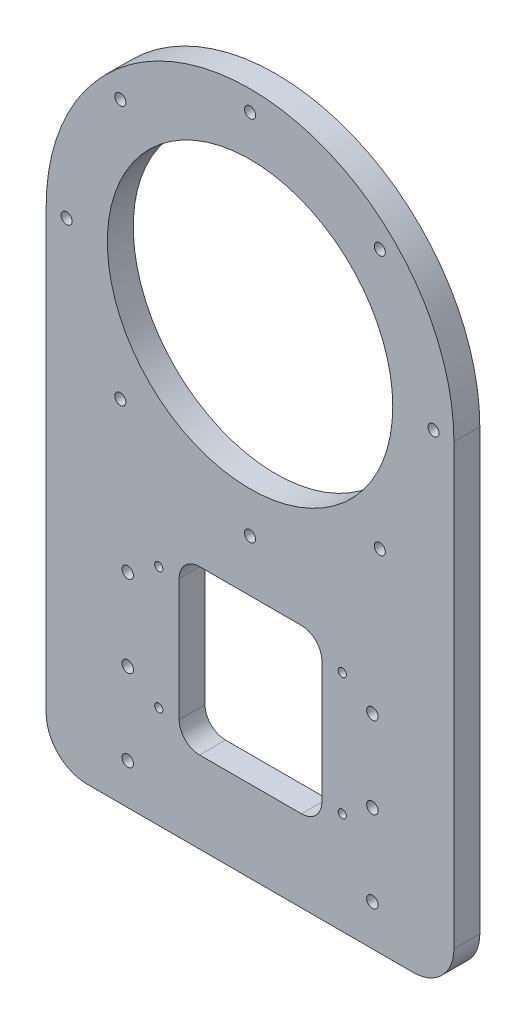
SolidWorks part; units mm, degrees
ref_plane "Front Plane" through (0, 0, 0) normal (0, 0, 1) x (1, 0, 0)
ref_plane "Top Plane" through (0, 0, 0) normal (0, 1, 0) x (1, 0, 0)
ref_plane "Right Plane" through (0, 0, 0) normal (1, 0, 0) x (0, 0, -1)
sketch "Sketch1" plane through (0, 0, 0) normal (0, 0, 1) x (1, 0, 0)
  circle A0 centre (0, 0) radius 35
  circle A1 centre (0, 0) radius 50
  dimension "D1" = 70
  dimension "D2" = 100
extrude "Boss-Extrude1" add sketch "Sketch1" along normal blind 6.35
sketch "Sketch2" plane through (0, 0, 6.35) normal (0, 0, 1) x (1, 0, 0)
  circle A0 centre (0, 0) radius 105
  dimension "D1" = 210
sketch "Sketch3" plane through (0, 0, 6.35) normal (0, 0, 1) x (1, 0, 0)
  line L0 (-50, 0) -> (-50, -117.7)
  line L1 (-50, -117.7) -> (50, -117.7)
  line L4 (0, -105) -> (0, -117.7) construction
  line L6 (137.4941, -68.35) -> (137.4941, -66.7834)
  line L14 (50, 0) -> (50, -117.7)
  circle A0 centre (0, 0) radius 50 construction
  circle A2 centre (0, 0) radius 105 construction
  arc A3 (-50, 0) -> (50, 0) centre (0, 0) ccw
  dimension "D3" = 12.7
extrude "Boss-Extrude2" add sketch "Sketch3" against normal up to surface (6.35 mm away) up to face at (50, 0, 0)
sketch "Sketch4" plane through (0, 0, 6.35) normal (0, 0, 1) x (1, 0, 0)
  circle A0 centre (0, 0) radius 35 construction
  point P0 (45, 0)
  point P3 (31.8198, -31.8198)
  point P6 (0, -45)
  point P7 (-31.8198, -31.8198)
  point P8 (-45, 0)
  point P9 (-31.8198, 31.8198)
  point P10 (0, 45)
  point P11 (31.8198, 31.8198)
  point P12 (0, 0)
  dimension "D1" = 45
  dimension "D2" = 8
hole_wizard "#6-32 Tapped Hole1" positions "Sketch5" profile "Sketch6" tap size "#6-32" standard "ANSI Inch" end condition through all
sketch "Sketch5" plane through (0, 0, 6.35) normal (0, 0, 1) x (1, 0, 0)
  point P0 (-45, 0)
  point P3 (-31.8198, -31.8198)
  point P6 (0, -45)
  point P9 (31.8198, -31.8198)
  point P12 (45, 0)
  point P15 (31.8198, 31.8198)
  point P18 (0, 45)
  point P21 (-31.8198, 31.8198)
sketch "Sketch6" plane through (-45, 0, 6.35) normal (1, 0, 0) x (0, -1, 0)
  line L0 (0, 0) -> (0, 6.35)
  line L1 (0, 6.35) -> (1.3525, 6.35)
  line L2 (1.3525, 6.35) -> (1.3525, 0)
  line L5 (1.3525, 0) -> (0, 0)
  line L11 (0, -6.35) -> (0, 107.95) construction
  dimension "Thru Tap Drill Dia." = 2.7051
  dimension "Thru Tap Drill Depth" = 6.35
cosmetic thread "Hole Thread1" parameters "D2"=3.5052
cosmetic thread "Hole Thread2" parameters "D2"=3.5052
cosmetic thread "Hole Thread3" parameters "D2"=3.5052
cosmetic thread "Hole Thread4" parameters "D2"=3.5052
cosmetic thread "Hole Thread5" parameters "D2"=3.5052
cosmetic thread "Hole Thread6" parameters "D2"=3.5052
cosmetic thread "Hole Thread7" parameters "D2"=3.5052
cosmetic thread "Hole Thread8" parameters "D2"=3.5052
fillet "Fillet1" radius 10 2 edges at (50, -117.7, 3.175) (-50, -117.7, 3.175)
sketch "Sketch7" plane through (0, 0, 6.35) normal (0, 0, 1) x (1, 0, 0)
  line L0 (0, -105) -> (0, -117.7) construction
  line L1 (-50, -117.7) -> (50, -117.7) construction
  point P0 (-30, -107.7)
  point P1 (30, -107.7)
  point P6 (-30, -67.7)
  point P7 (-30, -87.7)
  point P8 (30, -87.7)
  point P9 (30, -67.7)
  dimension "D1" = 60
  dimension "D2" = 30
  dimension "D3" = 10
  dimension "D4" = 10
  dimension "D5" = 2
  dimension "D6" = 2
hole_wizard "M4x0.7 Tapped Hole1" positions "Sketch8" profile "Sketch10" tap size "M4x0.7" standard "ANSI Metric" end condition through all
sketch "Sketch8" plane through (0, 0, 6.35) normal (0, 0, 1) x (1, 0, 0)
  point P0 (-30, -107.7)
  point P3 (30, -107.7)
  point P6 (30, -87.7)
  point P9 (-30, -87.7)
  point P13 (30, -67.7)
  point P16 (-30, -67.7)
sketch "Sketch10" plane through (-30, -107.7, 6.35) normal (1, 0, 0) x (0, -1, 0)
  line L0 (0, 0) -> (0, 6.35)
  line L1 (0, 6.35) -> (1.4, 6.35)
  line L2 (1.4, 6.35) -> (1.4, 0)
  line L5 (1.4, 0) -> (0, 0)
  line L11 (0, -6.35) -> (0, 107.95) construction
  dimension "Thru Tap Drill Dia." = 2.8
  dimension "Thru Tap Drill Depth" = 6.35
cosmetic thread "Hole Thread13" parameters "D2"=4
cosmetic thread "Hole Thread14" parameters "D2"=4
cosmetic thread "Hole Thread15" parameters "D2"=4
cosmetic thread "Hole Thread16" parameters "D2"=4
cosmetic thread "Hole Thread17" parameters "D2"=4
cosmetic thread "Hole Thread18" parameters "D2"=4
sketch "Sketch11" plane through (0, 0, 0) normal (0, 0, -1) x (-1, 0, 0)
  line L0 (50, -117.7) -> (-50, -117.7) construction
  line L1 (-17.61, -97.7) -> (17.39, -97.7)
  line L2 (-17.61, -97.7) -> (-17.61, -57.7)
  line L3 (-17.61, -57.7) -> (17.39, -57.7)
  line L4 (17.39, -97.7) -> (17.39, -57.7)
  line L5 (-17.61, -97.7) -> (17.39, -57.7) construction
  line L6 (-17.61, -57.7) -> (17.39, -97.7) construction
  point P0 (-0.11, -77.7)
  dimension "D1" = 40
  dimension "D2" = 35
  dimension "D3" = 40
extrude "Cut-Extrude1" cut sketch "Sketch11" against normal blind 10
fillet "Fillet2" radius 5 4 edges at (-17.39, -97.7, 3.175) (17.61, -97.7, 3.175) (17.61, -57.7, 3.175) (-17.39, -57.7, 3.175)
sketch "Sketch12" plane through (0, 0, 0) normal (0, 0, -1) x (-1, 0, 0)
  line L0 (-17.61, -62.7) -> (-17.61, -92.7) construction
  line L1 (-0.11, -97.7) -> (-0.11, -57.7) construction
  line L2 (-12.61, -97.7) -> (12.39, -97.7) construction
  line L3 (12.39, -57.7) -> (-12.61, -57.7) construction
  point P0 (-22.61, -62.7)
  point P1 (-22.61, -92.7)
  point P10 (22.39, -92.7)
  point P11 (22.39, -62.7)
  dimension "D1" = 5
  dimension "D2" = 5
hole_wizard "M3x0.5 Tapped Hole1" positions "Sketch13" profile "Sketch15" tap size "M3x0.5" standard "ANSI Metric" end condition through all
sketch "Sketch13" plane through (0, 0, 0) normal (0, 0, -1) x (-1, 0, 0)
  point P0 (-22.61, -62.7)
  point P3 (-22.61, -92.7)
  point P6 (22.39, -92.7)
  point P9 (22.39, -62.7)
sketch "Sketch15" plane through (22.61, -62.7, 0) normal (1, 0, 0) x (0, 1, 0)
  line L0 (0, 0) -> (0, 6.35)
  line L1 (0, 6.35) -> (1, 6.35)
  line L2 (1, 6.35) -> (1, 0)
  line L5 (1, 0) -> (0, 0)
  line L11 (0, -6.35) -> (0, 107.95) construction
  dimension "Thru Tap Drill Dia." = 2
  dimension "Thru Tap Drill Depth" = 6.35
cosmetic thread "Hole Thread9" parameters "D2"=3
cosmetic thread "Hole Thread10" parameters "D2"=3
cosmetic thread "Hole Thread11" parameters "D2"=3
cosmetic thread "Hole Thread12" parameters "D2"=3
